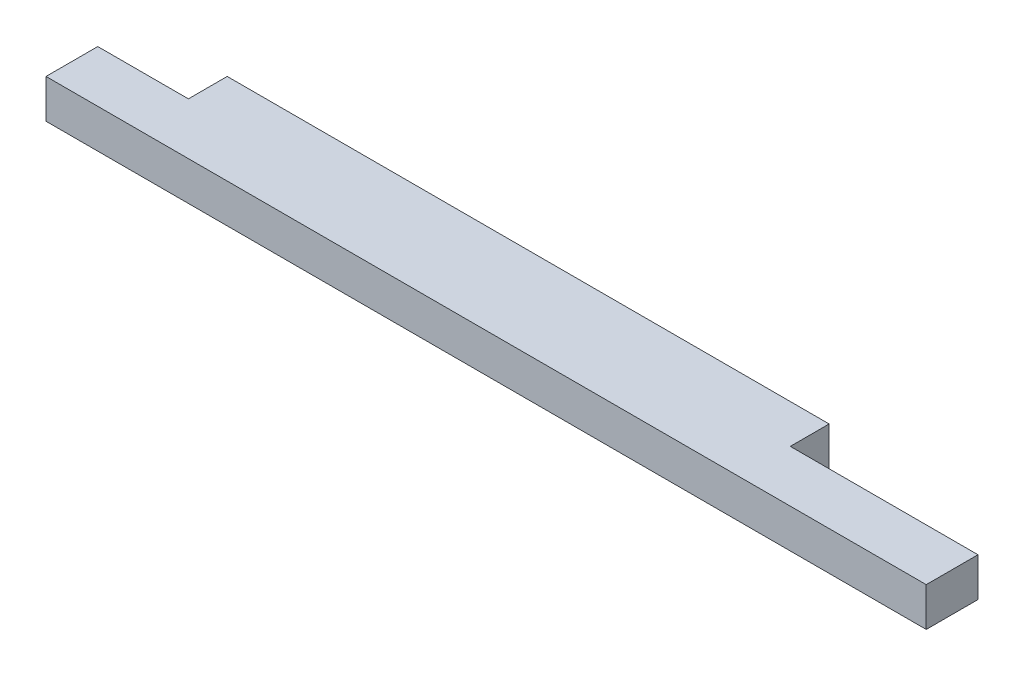
SolidWorks part; units mm, degrees
material "Pine"
ref_plane "Front Plane" through (0, 0, 0) normal (0, 0, 1) x (1, 0, 0)
ref_plane "Top Plane" through (0, 0, 0) normal (0, 1, 0) x (1, 0, 0)
ref_plane "Right Plane" through (0, 0, 0) normal (1, 0, 0) x (0, 0, -1)
sketch "Sketch1" plane through (0, 0, 0) normal (0, 1, 0) x (1, 0, 0)
  line L1 (0, 0) -> (863.6, 0)
  line L2 (0, 0) -> (0, 88.9)
  line L3 (0, 88.9) -> (863.6, 88.9)
  line L4 (863.6, 0) -> (863.6, 88.9)
  dimension "D1" = 88.9
  dimension "D2" = 863.6
extrude "Boss-Extrude1" add sketch "Sketch1" along normal blind 38.1
sketch "Sketch3" plane through (0, 38.1, 0) normal (0, 1, 0) x (1, 0, 0)
  line L5 (863.6, 88.9) -> (679.45, 88.9)
  line L6 (863.6, 88.9) -> (863.6, 50.8)
  line L7 (863.6, 50.8) -> (679.45, 50.8)
  line L8 (679.45, 88.9) -> (679.45, 50.8)
  dimension "D2" = 184.15
  dimension "D4" = 38.1
extrude "Cut-Extrude1" cut sketch "Sketch3" against normal through all
sketch "Sketch4" plane through (0, 38.1, 0) normal (0, 1, 0) x (1, 0, 0)
  line L0 (679.45, 88.9) -> (0, 88.9) construction
  line L1 (0, 88.9) -> (88.9, 88.9)
  line L2 (0, 88.9) -> (0, 50.8)
  line L3 (0, 50.8) -> (88.9, 50.8)
  line L4 (88.9, 88.9) -> (88.9, 50.8)
  dimension "D1" = 38.1
  dimension "D2" = 88.9
extrude "Cut-Extrude2" cut sketch "Sketch4" against normal through all
